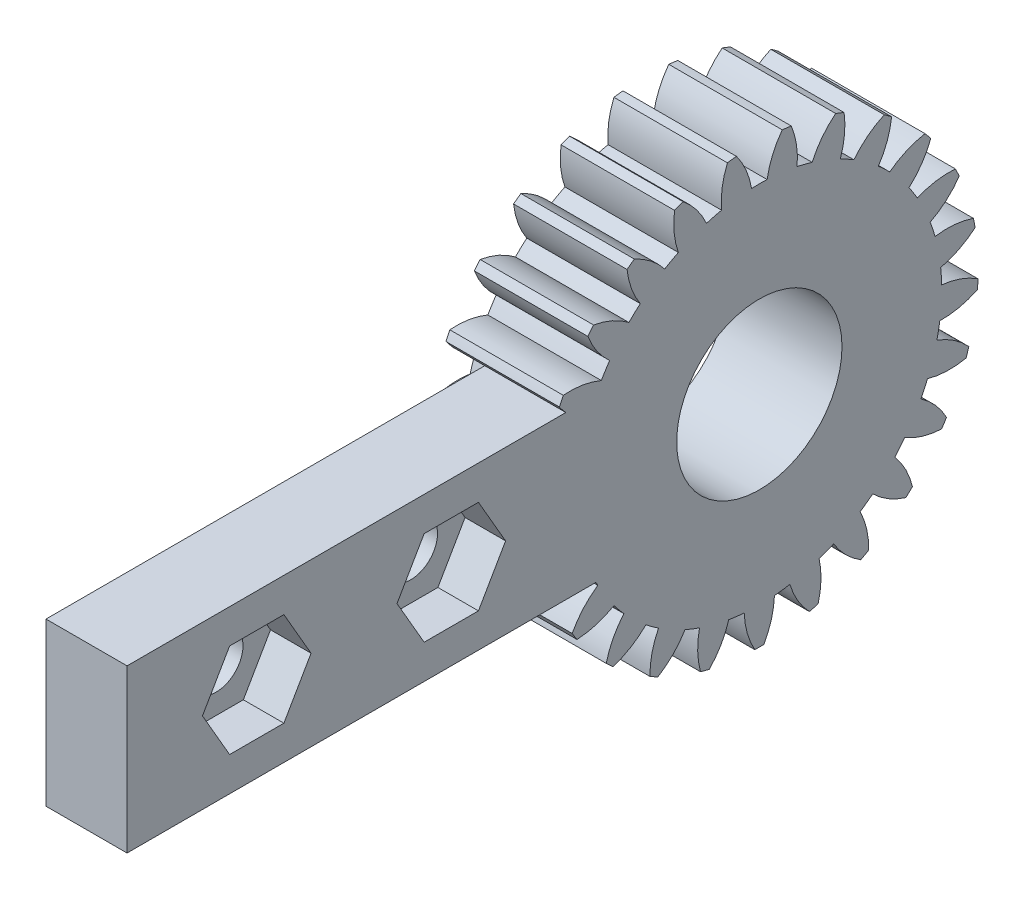
SolidWorks part; units mm, degrees
ref_plane "Plane1" through (0, 0, 0) normal (0, 0, 1) x (1, 0, 0)
ref_plane "Plane2" through (0, 0, 0) normal (0, 1, 0) x (1, 0, 0)
ref_plane "Plane3" through (0, 0, 0) normal (1, 0, 0) x (0, 0, -1)
sketch "HoldingSke" plane through (0, 0, 0) normal (0, 1, 0) x (1, 0, 0)
  line L0 (0, 0) -> (0.9063, -0.4226)
  line L1 (-15, 0) -> (100, 0) construction
  line L2 (0, 0) -> (-2.1039, 2.3779)
  line L3 (0, 0) -> (-11.863, 4.5341)
  line L4 (0, 0) -> (7.8269, 3.6497)
  line L5 (0, 0) -> (-46.8476, -17.4728)
  line L6 (0, 0) -> (-5.8027, -3.9151)
  line L7 (-2.1039, 2.3779) -> (8.6586, 51.2059)
  line L8 (-76.2, 54.61) -> (-76.1, 54.61)
  line L9 (-71.009, 38.7566) -> (-53.1078, 45.2721)
  line L10 (-76.2, 71.12) -> (104.1128, 71.12)
  line L11 (0, 0) -> (-7, 0)
  line L12 (-76.2, 101.6) -> (-76.162, 101.6)
  line L13 (24.9733, 27.94) -> (52.9518, 28.4284)
  line L14 (24.9733, 27.94) -> (24.9743, 27.94)
  line L15 (24.9733, 27.94) -> (100.4006, 29.5858)
  line L16 (-63.627, -1) -> (-12.827, -1)
  circle A0 centre (0, 0) radius 0.4
  circle A1 centre (0, 0) radius 11.249
  circle A2 centre (0, 0) radius 37.5
  circle A3 centre (0, 0) radius 0.4
  dimension "MHD" = 22.498
  dimension "Hub_dia" = 75
  dimension "Bore" = 0.8
  dimension "MBD" = 0.8
  dimension "Num_teeth" = 25
  dimension "Pitch" = 1
  dimension "Overall_len" = 50
  dimension "Show_teeth" = 25
  dimension "Thickness" = 7
  dimension "OAL" = 50.0001
  dimension "T_dim" = 0.1
  dimension "Ap" = 20
  dimension "H" = 19.05
  dimension "Pitch_radius" = 180.3128
  dimension "Width" = 7
  dimension "Backlash" = 0.038
  dimension "Addendum_fac" = 1
  dimension "Dedendum_fac" = 1.25
  dimension "Clearance_fac" = 0.25
  dimension "Dedendum_add" = 0.001
  dimension "Module" = 1
sketch "BasProSke" plane through (0, 0, 0) normal (0, 1, 0) x (1, 0, 0)
  line L0 (-10, 0) -> (60, 0) construction
  line L1 (0, 0) -> (0, 13.5)
  line L2 (0, 0) -> (7, 0)
  line L3 (7, 0) -> (7, 13.5)
  line L4 (7, 13.5) -> (0, 13.5)
  dimension "Thickness" = 7
  dimension "Diameter" = 27
revolve "Base-Revolve" add sketch "BasProSke" angle 360 about L0
sketch "TooCutSke" plane through (0, 0, 0) normal (1, 0, 0) x (0, 0, -1)
  line L1 (0, 0) -> (0, 107) construction
  line L2 (0, 0) -> (-0.8514, 12.471) construction
  line L3 (0, 0) -> (-3.1282, 24.7619) construction
  line L4 (-0.8514, 12.471) -> (-1.5641, 12.3809) construction
  arc A0 (0.4801, 11.2388) -> (-0.4801, 11.2388) centre (0, 0) ccw
  arc A1 (1.4322, 13.4494) -> (-1.4322, 13.4494) centre (0, 0) ccw
  circle A2 centre (0, 0) radius 12.5 construction
  circle A3 centre (0, 0) radius 11.7462 construction
  arc A4 (-0.4801, 11.2388) -> (-1.4322, 13.4494) centre (-5.4133, 10.4244) ccw
  arc A5 (1.4322, 13.4494) -> (0.4801, 11.2388) centre (5.4133, 10.4244) ccw
  dimension "Root_dia" = 22.498
  dimension "Overcut_dia" = 27.0508
  dimension "Pitch_dia" = 25
  dimension "Base_dia" = 23.4923
  dimension "Flank_rad" = 5
  dimension "Half_ang" = 7.2
  dimension "Half_CT" = 0.7184
extrude "ToothCut" cut sketch "TooCutSke" along normal through all
fillet "Breaks" [suppressed] radius 0.02
fillet "RootFillets" [suppressed] radius 0.251
pattern_circular "TeethCuts" count 25 every 14.4 about axis through (-10, 0, 0) along (1, 0, 0) of "ToothCut", "RootFillets", "Breaks"
sketch "HubNeaOneSke" plane through (0, 0, 0) normal (-1, 0, 0) x (0, 0, 1)
  circle A0 centre (0, 0) radius 11.249
  dimension "Diameter" = 22.498
extrude "HubNearOne" [suppressed] add sketch "HubNeaOneSke" along normal blind 43.0001
sketch "HubNeaBotSke" plane through (0, 0, 0) normal (-1, 0, 0) x (0, 0, 1)
  circle A0 centre (0, 0) radius 11.249
  dimension "Diameter" = 22.498
extrude "HubNearBoth" [suppressed] add sketch "HubNeaBotSke" along normal blind 21.5
ref_plane "FarPln" through (7, 0, 0) normal (1, 0, 0) x (0, 0, -1)
sketch "HubFarSke" plane through (7, 0, 0) normal (1, 0, 0) x (0, 0, -1)
  circle A0 centre (0, 0) radius 11.249
  dimension "Diameter" = 22.498
extrude "HubFar" [suppressed] add sketch "HubFarSke" along normal blind 21.5
sketch "BorSke" plane through (0, 0, 0) normal (1, 0, 0) x (0, 0, -1)
  circle A0 centre (0, 0) radius 0.4
  dimension "Diameter" = 0.8
extrude "Bore" cut sketch "BorSke" along normal mid plane 100.0001
sketch "KeySke" plane through (0, 0, 0) normal (1, 0, 0) x (0, 0, -1)
  line L0 (-0.05, 0) -> (-0.05, 0.5)
  line L1 (-0.05, 0.5) -> (0.05, 0.5)
  line L2 (0.05, 0.5) -> (0.05, 0)
  line L3 (0, 0) -> (0, 34) construction
  line L4 (-0.05, 0) -> (0.05, 0)
  dimension "Offset" = 0.5
  dimension "Width" = 0.1
extrude "Keyway" [suppressed] cut sketch "KeySke" along normal mid plane 100.0001
pattern_circular "Keyway2" [suppressed] count 2 every 90 about axis through (-10, 0, 0) along (1, 0, 0)
sketch "草图1" plane through (7, 0, 0) normal (1, 0, 0) x (0, 0, -1)
  circle A0 centre (0, 0) radius 5.1
  dimension "D1" = 10.2
extrude "切除-拉伸1" cut sketch "草图1" against normal blind 10
sketch "草图2" plane through (7, 0, 0) normal (1, 0, 0) x (0, 0, -1)
  line L1 (-9, 5) -> (-39, 5)
  line L2 (-9, 5) -> (-9, -5)
  line L3 (-9, -5) -> (-39, -5)
  line L4 (-39, 5) -> (-39, -5)
  circle A0 centre (0, 0) radius 5.1 construction
  circle A1 centre (-31, 0) radius 1.65
  circle A2 centre (-19, 0) radius 1.65
  dimension "D7" = 3.3
  dimension "D8" = 3.3
  dimension "D1" = 5
  dimension "D2" = 10
  dimension "D3" = 9
  dimension "D4" = 30
  dimension "D5" = 8
  dimension "D6" = 12
  dimension "D9" = 5
extrude "凸台-拉伸2" add sketch "草图2" against normal blind 5
sketch "草图3" plane through (7, 0, 0) normal (1, 0, 0) x (0, 0, -1)
  line L1 (-27.6514, 0) -> (-29.3257, 2.9)
  line L2 (-29.3257, 2.9) -> (-32.6743, 2.9)
  line L3 (-32.6743, 2.9) -> (-34.3486, 0)
  line L4 (-34.3486, 0) -> (-32.6743, -2.9)
  line L5 (-32.6743, -2.9) -> (-29.3257, -2.9)
  line L6 (-29.3257, -2.9) -> (-27.6514, 0)
  line L7 (-15.6514, 0) -> (-17.3257, 2.9)
  line L8 (-17.3257, 2.9) -> (-20.6743, 2.9)
  line L9 (-20.6743, 2.9) -> (-22.3486, 0)
  line L10 (-22.3486, 0) -> (-20.6743, -2.9)
  line L11 (-20.6743, -2.9) -> (-17.3257, -2.9)
  line L12 (-17.3257, -2.9) -> (-15.6514, 0)
  circle A0 centre (-31, 0) radius 2.9 construction
  circle A1 centre (-19, 0) radius 2.9 construction
  dimension "D1" = 5.8
  dimension "D2" = 5.8
extrude "切除-拉伸2" cut sketch "草图3" against normal blind 2.5
equation "' \"Module@HoldingSke\" = 6.35"
equation "' \"Num_teeth@HoldingSke\" = 12"
equation "' \"Ap@HoldingSke\" =  20"
equation "' \"Ap@HoldingSke\" = 20"
equation "' \"Width@HoldingSke\" = 0.5 * 25.4"
equation "' \"Hub_dia@HoldingSke\"= 1 * 25.4"
equation "' \"Hub_dia@HoldingSke\" = 1 * 25.4"
equation "' \"Overall_len@HoldingSke\" = 1.0 * 25.4"
equation "' \"Bore@HoldingSke\" = 0.75 * 25.4"
equation "' \"T_dim@HoldingSke\" = 0.1 * 25.4"
equation "' \"Width@KeySke\" = 0.25 * 25.4"
equation "' \"Show_teeth@HoldingSke\" = 13"
equation "' \"Backlash@HoldingSke\" = 0.009 * 25.4"
equation "' \"Addendum_fac@HoldingSke\" = 1.0"
equation "' \"Dedendum_fac@HoldingSke\" = 1.25"
equation "' \"Dedendum_add@HoldingSke\" = 0.00005 * 25.4"
equation "' \"Clearance_fac@HoldingSke\" = 0.25"
equation "\"Pitch@HoldingSke\" = 1 / \"Module@HoldingSke\""
equation "\"Overcut_dia@TooCutSke\" = (\"Num_teeth@HoldingSke\" + 2 * \"Addendum_fac@HoldingSke\") / \"Pitch@HoldingSke\" + 0.002 * 25.4"
equation "\"Pitch_dia@TooCutSke\" = \"Num_teeth@HoldingSke\" / \"Pitch@HoldingSke\""
equation "\"Base_dia@TooCutSke\" = \"Num_teeth@HoldingSke\" / \"Pitch@HoldingSke\" * cos((\"Ap@HoldingSke\"  * 3.14159265 / 180))"
equation "\"Root_dia@TooCutSke\" = (\"Num_teeth@HoldingSke\" + 2) / \"Pitch@HoldingSke\" - 2 * (\"Addendum_fac@HoldingSke\" + \"Dedendum_fac@HoldingSke\") / \"Pitch@HoldingSke\" - \"Dedendum_add@HoldingSke\" * 2"
equation "\"Half_ang@TooCutSke\" = 180 / \"Num_teeth@HoldingSke\""
equation "\"Half_CT@TooCutSke\" = \"Num_teeth@HoldingSke\" / \"Pitch@HoldingSke\" * sin((3.14159265 / 2 / \"Num_teeth@HoldingSke\")) / 2 - 7 * \"Backlash@HoldingSke\" / 4"
equation "\"Flank_rad@TooCutSke\" = \"Num_teeth@HoldingSke\" / \"Pitch@HoldingSke\" / 5"
equation "\"Radius@RootFillets\" = \"Clearance_fac@HoldingSke\" / \"Pitch@HoldingSke\" + \"Dedendum_add@HoldingSke\""
equation "\"Break_rad@Breaks\" = 0.02 / \"Pitch@HoldingSke\""
equation "\"Thickness@HoldingSke\" = \"Width@HoldingSke\""
equation "\"OAL@HoldingSke\" = \"Thickness@HoldingSke\""
equation "\"MHD@HoldingSke\" = (\"Num_teeth@HoldingSke\" + 2) / \"Pitch@HoldingSke\" - 2 * (\"Addendum_fac@HoldingSke\" + \"Dedendum_fac@HoldingSke\")  / \"Pitch@HoldingSke\" - \"Dedendum_add@HoldingSke\" * 2"
equation "\"MBD@HoldingSke\" = (\"Num_teeth@HoldingSke\" + 2) / \"Pitch@HoldingSke\" - 2 * (\"Addendum_fac@HoldingSke\" + \"Dedendum_fac@HoldingSke\")  / \"Pitch@HoldingSke\" - \"Dedendum_add@HoldingSke\" * 2 - 0.002 * 25.4"
equation "\"MHD@HoldingSke\" = ((sgn( \"MHD@HoldingSke\" - \"Hub_dia@HoldingSke\" )-1)*( \"MHD@HoldingSke\" - \"Hub_dia@HoldingSke\" ))/-2+ \"Hub_dia@HoldingSke\""
equation "\"MBD@HoldingSke\" = ((sgn( \"MBD@HoldingSke\" - \"Bore@HoldingSke\" )-1)*( \"MBD@HoldingSke\" - \"Bore@HoldingSke\" ))/-2+ \"Bore@HoldingSke\""
equation "\"OAL@HoldingSke\" = ((sgn( \"OAL@HoldingSke\" - \"Overall_len@HoldingSke\" )+1)*( \"OAL@HoldingSke\" - \"Overall_len@HoldingSke\" ))/2 + \"Overall_len@HoldingSke\" + 0.000002 * 25.4"
equation "\"Num_teeth@TeethCuts\" = int( \"Show_teeth@HoldingSke\" ) + 1"
equation "\"Num_teeth@TeethCuts\" = ((sgn( \"Num_teeth@TeethCuts\" - \"Num_teeth@HoldingSke\" )-1)*( \"Num_teeth@TeethCuts\" - \"Num_teeth@HoldingSke\" ))/-2+ \"Num_teeth@HoldingSke\""
equation "\"Num_teeth@TeethCuts\" = ((sgn( \"Num_teeth@TeethCuts\" - 2.0)+1)*( \"Num_teeth@TeethCuts\" - 2.0))/2 +2.0"
equation "\"Angle@TeethCuts\" = 360.0 / \"Num_teeth@HoldingSke\""
equation "\"Diameter@BasProSke\" = (\"Num_teeth@HoldingSke\" + 2 * \"Addendum_fac@HoldingSke\") / \"Pitch@HoldingSke\""
equation "\"Thickness@BasProSke\"  = \"Thickness@HoldingSke\""
equation "' \"Fillet_rad@BasProSke\" =  \"Thickness@HoldingSke\" * 0.05"
equation "' \"Fillet_rad@BasProSke\" = \"Thickness@HoldingSke\" * 0.05"
equation "\"MHD@HoldingSke\" = ((sgn( \"MHD@HoldingSke\" - \"Root_dia@TooCutSke\" )-1)*( \"MHD@HoldingSke\" - \"Root_dia@TooCutSke\" ))/-2+ \"Root_dia@TooCutSke\""
equation "\"Diameter@HubNeaOneSke\" = \"MHD@HoldingSke\""
equation "\"Length@HubNearOne\" = \"OAL@HoldingSke\" - \"Thickness@BasProSke\""
equation "\"Diameter@HubNeaBotSke\" = \"MHD@HoldingSke\""
equation "\"Length@HubNearBoth\" = ( \"OAL@HoldingSke\" - \"Thickness@BasProSke\" ) / 2.0"
equation "\"Thickness@FarPln\" = \"Thickness@BasProSke\""
equation "\"Diameter@HubFarSke\" = \"MHD@HoldingSke\""
equation "\"Length@HubFar\" = ( \"OAL@HoldingSke\" - \"Thickness@BasProSke\" ) / 2.0"
equation "\"Diameter@BorSke\" = \"MBD@HoldingSke\""
equation "\"D1@Bore\" = \"OAL@HoldingSke\" * 2.0"
equation "\"D1@Keyway\" = \"OAL@HoldingSke\" * 2.0"
equation "\"Offset@KeySke\" = \"T_dim@HoldingSke\" + \"MBD@HoldingSke\" / 2.0"
